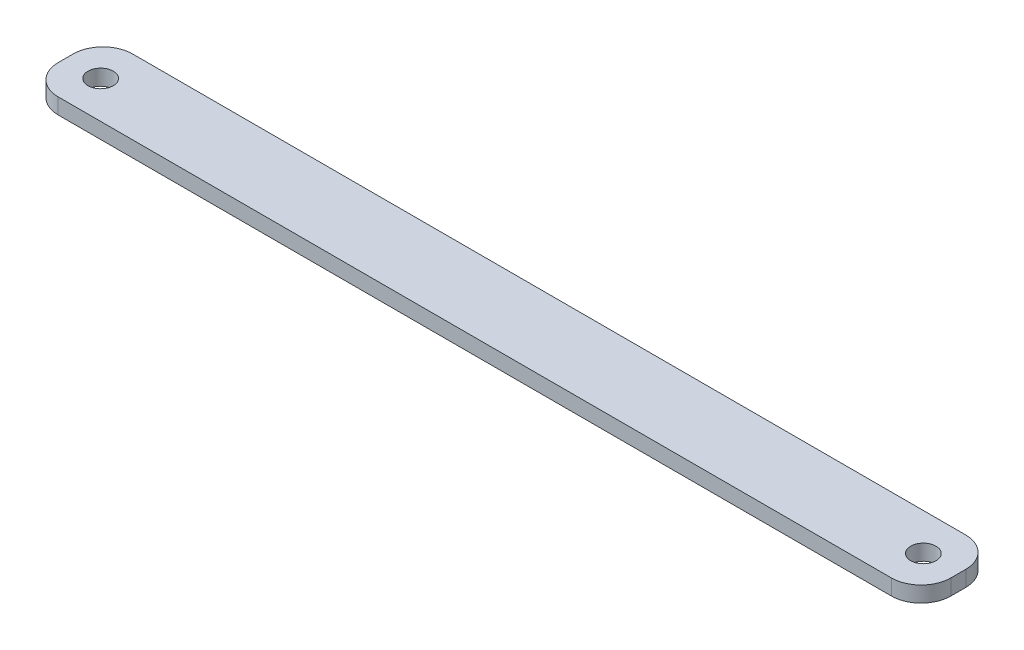
SolidWorks part; units mm, degrees
ref_plane "Alzado" through (0, 0, 0) normal (0, 0, 1) x (1, 0, 0)
ref_plane "Planta" through (0, 0, 0) normal (0, 1, 0) x (1, 0, 0)
ref_plane "Vista lateral" through (0, 0, 0) normal (1, 0, 0) x (0, 0, -1)
sketch "Croquis1" plane through (0, 0, 0) normal (0, 1, 0) x (1, 0, 0)
  line L0 (0, 0) -> (0, 7.2489) construction
  line L1 (-60, 5) -> (60, 5)
  line L2 (-60, 5) -> (-60, -5)
  line L3 (-60, -5) -> (60, -5)
  line L4 (60, 5) -> (60, -5)
  line L5 (-60, 5) -> (60, -5) construction
  line L6 (-60, -5) -> (60, 5) construction
  circle A0 centre (-55.3, 0) radius 1.7
  circle A1 centre (55.3, 0) radius 1.7
  point P0 (0, 0)
  dimension "D3" = 3.4
  dimension "D1" = 120
  dimension "D2" = 10
  dimension "D4" = 4.7
extrude "Saliente-Extruir1" add sketch "Croquis1" along normal blind 2.11
fillet "Redondeo1" radius 4 4 edges at (60, 1.055, -5) (60, 1.055, 5) (-60, 1.055, -5) (-60, 1.055, 5)
